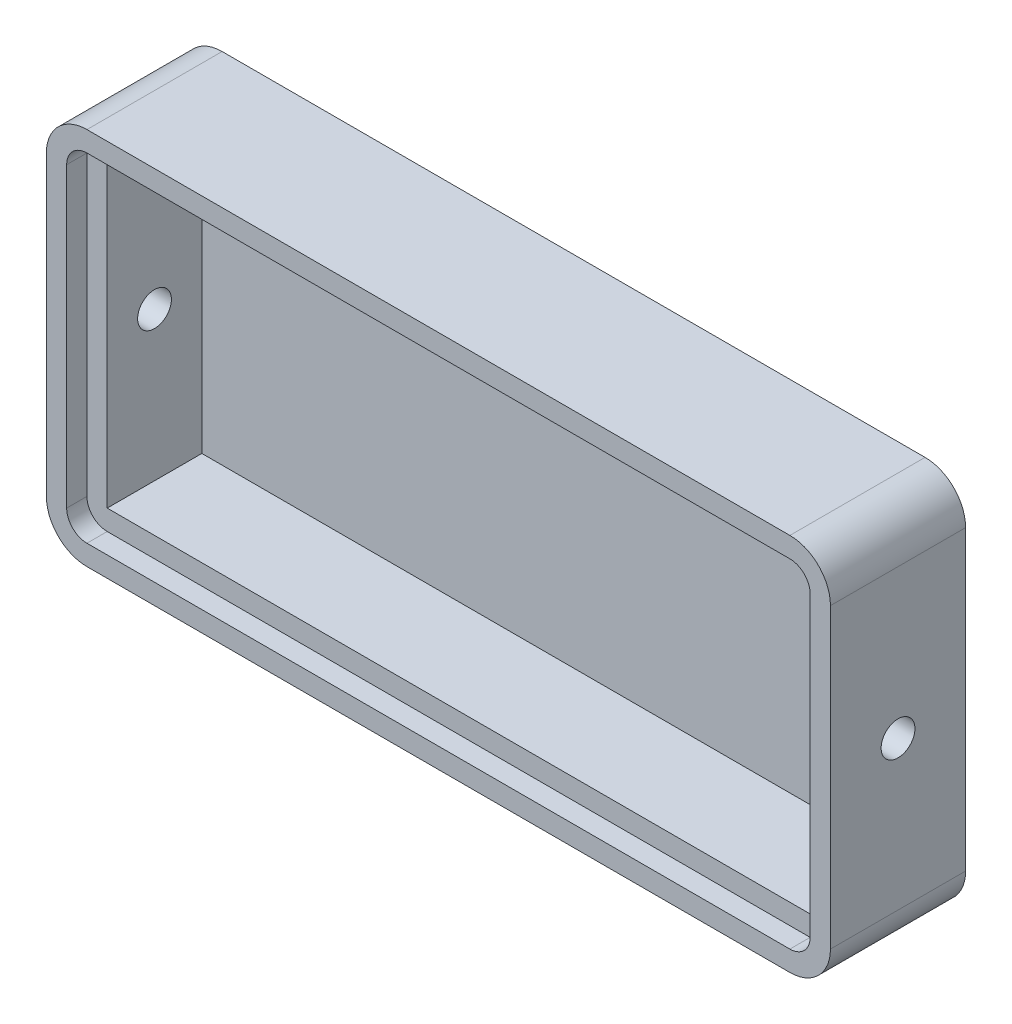
SolidWorks part; units mm, degrees
ref_plane "Plan de face" through (0, 0, 0) normal (0, 0, 1) x (1, 0, 0)
ref_plane "Plan de dessus" through (0, 0, 0) normal (0, 1, 0) x (1, 0, 0)
ref_plane "Plan de droite" through (0, 0, 0) normal (1, 0, 0) x (0, 0, -1)
sketch "Esquisse1" plane through (0, 0, 0) normal (0, 0, 1) x (1, 0, 0)
  line L1 (-58, 28) -> (58, 28)
  line L2 (-58, 28) -> (-58, -28)
  line L3 (-58, -28) -> (58, -28)
  line L4 (58, 28) -> (58, -28)
  line L5 (-58, 28) -> (58, -28) construction
  line L6 (-58, -28) -> (58, 28) construction
  point P0 (0, 0)
  point P6 (0, 0)
  dimension "D1" = 116
  dimension "D2" = 56
extrude "Boss.-Extru.1" add sketch "Esquisse1" along normal blind 20
fillet "Congé1" radius 6 4 edges at (58, 28, 10) (58, -28, 10) (-58, 28, 10) (-58, -28, 10)
shell "Coque1" thickness 3
sketch "Esquisse2" plane through (0, 0, 3) normal (0, 0, 1) x (1, 0, 0)
  line L0 (52, 22) -> (-52, 22)
  line L1 (-52, 22) -> (-52, -22)
  line L2 (-52, -22) -> (52, -22)
  line L3 (52, -22) -> (52, 22)
  line L4 (52, 25) -> (-52, 25)
  line L5 (-55, 22) -> (-55, -22)
  line L6 (-52, -25) -> (52, -25)
  line L7 (55, -22) -> (55, 22)
  line L8 (52, 25) -> (-52, 25)
  line L9 (-55, 22) -> (-55, -22)
  line L10 (-52, -25) -> (52, -25)
  line L11 (55, -22) -> (55, 22)
  arc A0 (-52, 22) -> (-52, 22) centre (-52, 22) ccw
  arc A1 (-52, -22) -> (-52, -22) centre (-52, -22) ccw
  arc A2 (52, -22) -> (52, -22) centre (52, -22) ccw
  arc A3 (52, 22) -> (52, 22) centre (52, 22) ccw
  arc A4 (-52, 25) -> (-55, 22) centre (-52, 22) ccw
  arc A5 (-55, -22) -> (-52, -25) centre (-52, -22) ccw
  arc A6 (52, -25) -> (55, -22) centre (52, -22) ccw
  arc A7 (55, 22) -> (52, 25) centre (52, 22) ccw
  arc A8 (-52, 25) -> (-55, 22) centre (-52, 22) ccw
  arc A9 (-55, -22) -> (-52, -25) centre (-52, -22) ccw
  arc A10 (52, -25) -> (55, -22) centre (52, -22) ccw
  arc A11 (55, 22) -> (52, 25) centre (52, 22) ccw
  dimension "D1" = 0
  dimension "D2" = 3
extrude "Boss.-Extru.2" add sketch "Esquisse2" along normal offset from surface (14 mm away) 3 up to face at (0, 0, 20)
sketch "Esquisse3" plane through (-58, 0, 0) normal (-1, 0, 0) x (0, 0, 1)
  line L0 (0, 22) -> (20, -22) construction
  circle A0 centre (10, 0) radius 2.5
  dimension "D1" = 5
extrude "Enlèv. mat.-Extru.1" cut sketch "Esquisse3" against normal through all
